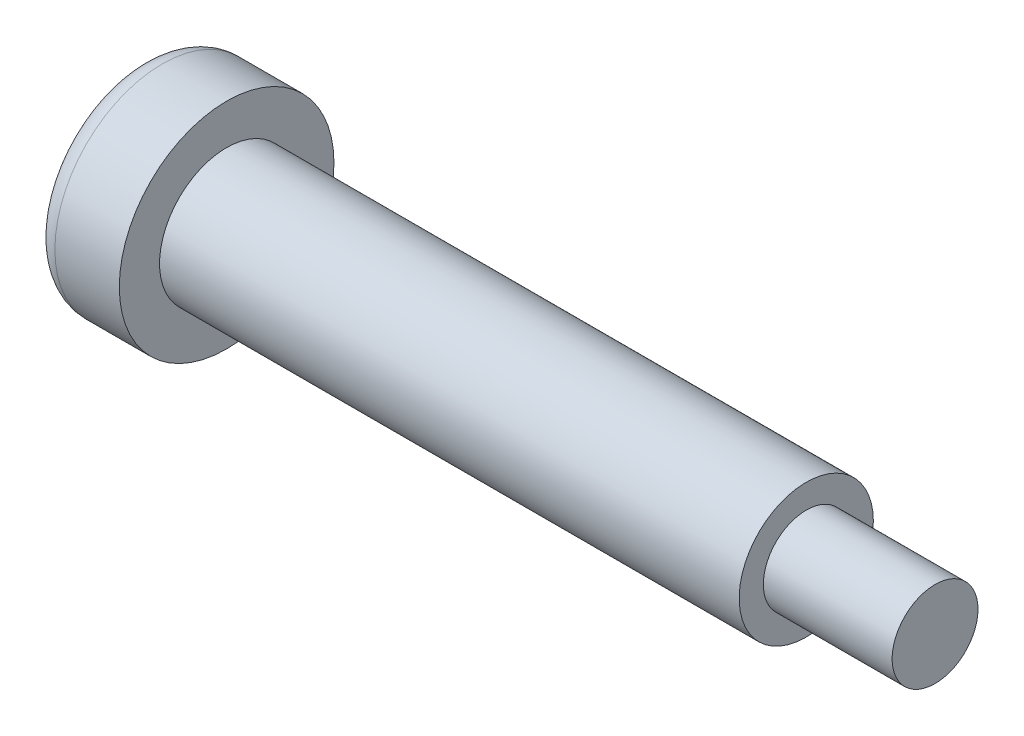
SolidWorks part; units mm, degrees
ref_plane "Front Plane" through (0, 0, 0) normal (0, 0, 1) x (1, 0, 0)
ref_plane "Top Plane" through (0, 0, 0) normal (0, 1, 0) x (1, 0, 0)
ref_plane "Right Plane" through (0, 0, 0) normal (1, 0, 0) x (0, 0, -1)
sketch "Sketch2" plane through (0, 0, 0) normal (1, 0, 0) x (0, 0, -1)
  circle A0 centre (0, 0) radius 5
extrude "Boss-Extrude1" add sketch "Sketch2" along normal blind 4
fillet "Fillet1" radius 1 1 edges at (0, 0, -5)
sketch "Sketch3" plane through (0, 0, 0) normal (-1, 0, 0) x (0, 0, 1)
  line L1 (2.076, 1.0117) -> (0.1618, 2.3037)
  line L2 (0.1618, 2.3037) -> (-1.9142, 1.292)
  line L3 (-1.9142, 1.292) -> (-2.076, -1.0117)
  line L4 (-2.076, -1.0117) -> (-0.1618, -2.3037)
  line L5 (-0.1618, -2.3037) -> (1.9142, -1.292)
  line L6 (1.9142, -1.292) -> (2.076, 1.0117)
  circle A0 centre (0, 0) radius 2 construction
  dimension "D1" = 4
extrude "Cut-Extrude2" cut sketch "Sketch3" against normal blind 2.5
sketch "Sketch4" plane through (4, 0, 0) normal (1, 0, 0) x (0, 0, -1)
  circle A0 centre (0, 0) radius 3.125
extrude "Boss-Extrude3" add sketch "Sketch4" along normal blind 33
sketch "Sketch5" plane through (37, 0, 0) normal (1, 0, 0) x (0, 0, -1)
  circle A0 centre (0, 0) radius 3.125
  circle A1 centre (0, 0) radius 2
extrude "Cut-Extrude4" cut sketch "Sketch5" against normal blind 6
